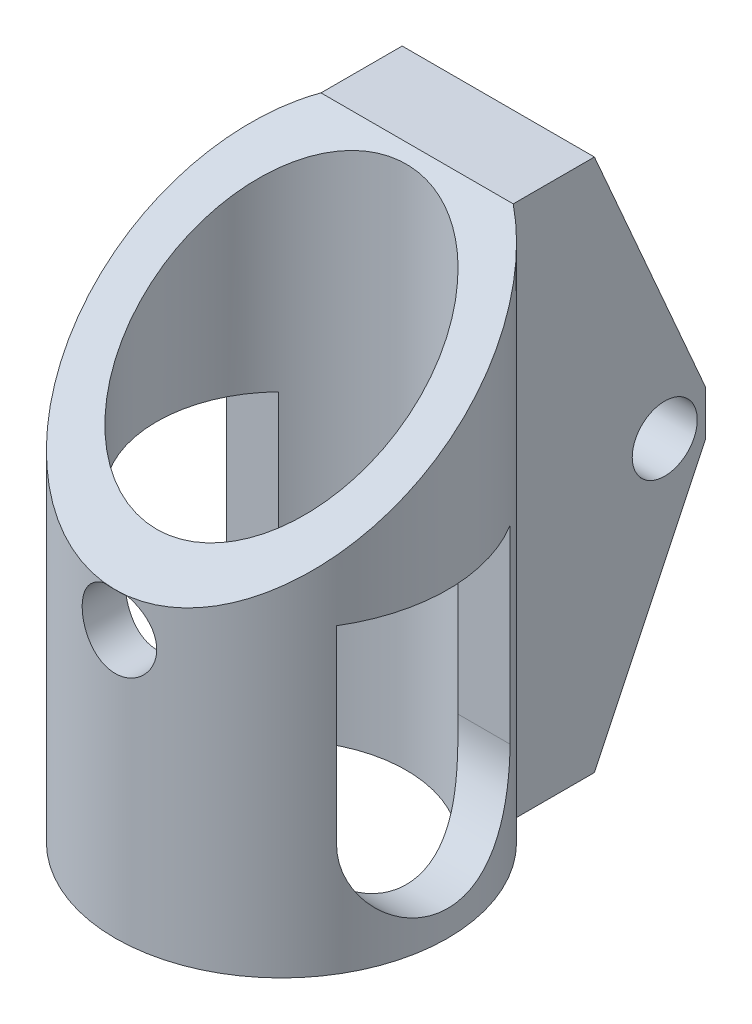
SolidWorks part; units mm, degrees
ref_plane "Front Plane" through (0, 0, 0) normal (0, 0, 1) x (1, 0, 0)
ref_plane "Top Plane" through (0, 0, 0) normal (0, 1, 0) x (1, 0, 0)
ref_plane "Right Plane" through (0, 0, 0) normal (1, 0, 0) x (0, 0, -1)
sketch "Sketch1" plane through (0, 0, 0) normal (0, 1, 0) x (1, 0, 0)
  circle A0 centre (0, 0) radius 8.6383
  circle A1 centre (0, 0) radius 11.5
  dimension "D1" = 17.2766
  dimension "D2" = 23
extrude "Boss-Extrude1" add sketch "Sketch1" along normal blind 36.88
ref_plane "Plane1" through (-11.5, 0, 0) normal (-1, 0, 0) x (0, 0, 1)
sketch "Sketch2" plane through (-11.5, 0, 0) normal (-1, 0, 0) x (0, 0, 1)
  line L0 (0, 29.0959) -> (0, 7.7841) construction
  line L1 (6, 29.0959) -> (6, 7.7841)
  line L2 (-6, 29.0959) -> (-6, 7.7841)
  line L3 (0, 29.0959) -> (0, 36.88) construction
  line L4 (8.6383, 36.88) -> (-8.6383, 36.88) construction
  line L5 (0, 7.7841) -> (0, 0) construction
  arc A0 (6, 29.0959) -> (-6, 29.0959) centre (0, 29.0959) ccw
  arc A1 (-6, 7.7841) -> (6, 7.7841) centre (0, 7.7841) ccw
  point P3 (0, 18.44)
  dimension "D1" = 6
extrude "Cut-Extrude1" cut sketch "Sketch2" against normal blind 55.88
sketch "Sketch3" plane through (0, 0, 0) normal (0, 0, 1) x (1, 0, 0)
  line L0 (0, 36.88) -> (0, 18.44) construction
  line L1 (11.5, 36.88) -> (-11.5, 36.88) construction
  circle A0 centre (0, 18.44) radius 2.5797
  dimension "D1" = 5.1594
  dimension "D2" = 18.44
extrude "Cut-Extrude2" cut sketch "Sketch3" along normal through all
sketch "Sketch4" plane through (0, 0, 0) normal (0, 0, 1) x (1, 0, 0)
  line L0 (-8.6383, 0) -> (-6.6495, 0) construction
  line L5 (8.6383, 0) -> (6.6495, 0) construction
  line L6 (8.6383, 36.88) -> (6.6495, 36.88) construction
  line L7 (-8.6383, 36.88) -> (-6.6495, 36.88) construction
  line L9 (6.6495, 0) -> (-6.6495, 0)
  line L10 (6.6495, 0) -> (6.6495, 36.88)
  line L11 (6.6495, 36.88) -> (-6.6495, 36.88)
  line L12 (-6.6495, 0) -> (-6.6495, 36.88)
  dimension "D1" = 6.6495
  dimension "D2" = 8.6383
  dimension "D3" = 6.6495
  dimension "D4" = 36.88
extrude "Boss-Extrude2" add sketch "Sketch4" along normal up to surface (5.6174 mm away) from offset 15
sketch "Sketch5" plane through (-6.6495, 0, 0) normal (-1, 0, 0) x (0, 0, 1)
  line L0 (-22.694, 16.1362) -> (-22.694, 19.234)
  line L1 (-15, 36.88) -> (-22.694, 19.234)
  line L2 (-22.694, 16.1362) -> (-15, 0)
  line L3 (-15, 17.577) -> (-19.8654, 17.577) construction
  line L4 (-15, 36.88) -> (-15, 0) construction
  circle A0 centre (-19.8654, 17.577) radius 2.25
  point P6 (-22.2657, 17.577)
  line M4 (-15, 36.88) -> (-15, 0)
  dimension "D1" = 4.5
extrude "Boss-Extrude3" add sketch "Sketch5" along direction (-1, 0, 0) on the side against the normal up to surface (13.299 mm away) contours L0 L2 L1 A0 M4
sketch "Sketch6" plane through (0, 36.88, 0) normal (0, 1, 0) x (1, 0, 0)
  line L1 (6.6495, 9.3826) -> (6.6495, 15) construction
  line L2 (11.9842, 3.302) -> (-11.7428, 3.302)
  line L3 (11.9842, 3.302) -> (11.9842, -12.5856)
  line L4 (11.9842, -12.5856) -> (-11.7428, -12.5856)
  line L5 (-11.7428, 3.302) -> (-11.7428, -12.5856)
  line L6 (6.6495, 15) -> (-6.6495, 15) construction
  dimension "D1" = 5.3347
  dimension "D2" = 18.3923
  dimension "D3" = 11.698
  dimension "D4" = 27.5856
extrude "Cut-Extrude3" cut sketch "Sketch6" against normal blind 15
sketch "Sketch7" plane through (0, 21.88, 0) normal (0, 1, 0) x (1, 0, 0)
  circle A0 centre (0, 0) radius 11.5
  circle A1 centre (0, 0) radius 8.6383
extrude "Boss-Extrude4" add sketch "Sketch7" against normal blind 1
sketch "Sketch8" plane through (0, 21.88, 0) normal (0, 1, 0) x (1, 0, 0)
  circle A0 centre (0, 0) radius 11.5
  circle A1 centre (0, 0) radius 8.6383
extrude "Boss-Extrude5" add sketch "Sketch8" along normal up to surface (15 mm away) up to face at (0, 36.88, -8.505)
sketch "Sketch9" plane through (-11.5, 0, 0) normal (-1, 0, 0) x (0, 0, 1)
  line L0 (-9.3826, 36.88) -> (11.5, 20.88)
  line L1 (11.5, 20.88) -> (11.5, 36.88) construction
  line L2 (11.5, 20.88) -> (11.5, 36.88)
  line L3 (11.5, 36.88) -> (-9.3826, 36.88)
  dimension "D1" = 20.88
extrude "Cut-Extrude4" cut sketch "Sketch9" against normal through all
